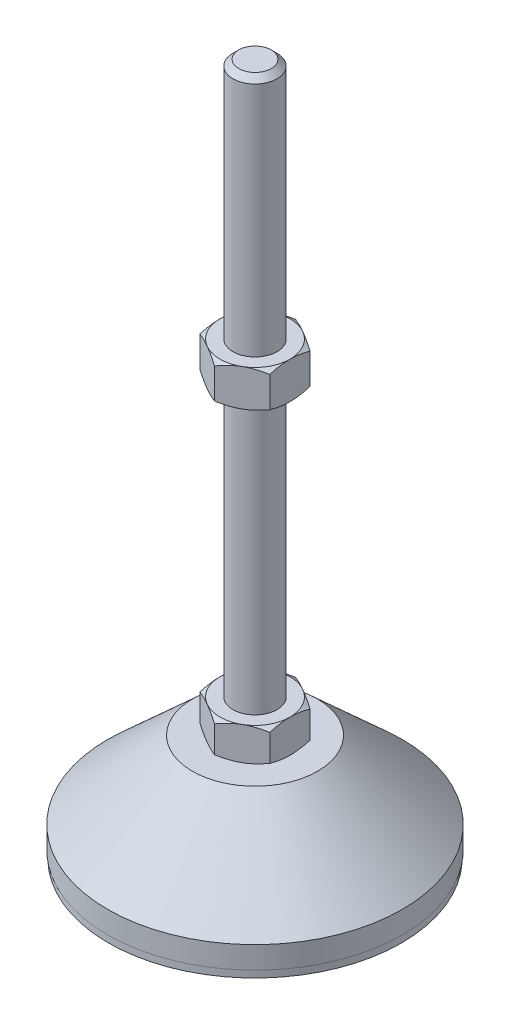
SolidWorks part; units mm, degrees
ref_plane "Спереди" through (0, 0, 0) normal (0, 0, 1) x (1, 0, 0)
ref_plane "Сверху" through (0, 0, 0) normal (0, 1, 0) x (1, 0, 0)
ref_plane "Справа" through (0, 0, 0) normal (1, 0, 0) x (0, 0, -1)
sketch "Эскиз1" plane through (0, 0, 0) normal (0, 0, 1) x (1, 0, 0)
  line L0 (0, 0) -> (-39.8, 0)
  line L1 (-39.8, 0) -> (-39.8, 2)
  line L2 (-39.8, 2) -> (-40, 2)
  line L3 (-40, 2) -> (-40, 8)
  line L4 (-40, 8) -> (-17, 29)
  line L5 (-17, 29) -> (-6, 29)
  line L12 (-6, 38) -> (-6, 186.4)
  line L13 (-6, 186.4) -> (-4.4, 188)
  line L14 (-4.4, 188) -> (0, 188)
  line L15 (0, 188) -> (0, 0) construction
  line L16 (-6, 29) -> (0, 29) construction
  line L17 (0, 0) -> (0, 188)
  line L18 (0, 0) -> (0, -7.9595) construction
  line L19 (-6, 38) -> (-6, 29)
  point P8 (-6, 112.2)
  point P23 (-11.5, 29)
  dimension "D1" = 12
  dimension "D2" = 29
  dimension "D3" = 9
  dimension "D4" = 80
  dimension "D5" = 6
  dimension "D6" = 1.6
  dimension "D7" = 45
  dimension "D8" = 34
  dimension "D9" = 2
  dimension "D10" = 150
  dimension "D11" = 6
  dimension "D12" = 0.2
revolve "Повернуть1" add sketch "Эскиз1" angle 360 about L17
sketch "Эскиз2" plane through (0, 29, 0) normal (0, 1, 0) x (1, 0, 0)
  line L1 (0, 10.9697) -> (-9.5, 5.4848)
  line L2 (-9.5, 5.4848) -> (-9.5, -5.4848)
  line L3 (-9.5, -5.4848) -> (0, -10.9697)
  line L4 (0, -10.9697) -> (9.5, -5.4848)
  line L5 (9.5, -5.4848) -> (9.5, 5.4848)
  line L6 (9.5, 5.4848) -> (0, 10.9697)
  circle A0 centre (0, 0) radius 9.5 construction
  dimension "D1" = 19
extrude "Бобышка-Вытянуть1" add sketch "Эскиз2" along normal up to vertex (9 mm away) up to point (-6, 38, 0)
ref_plane "Плоскость1" through (0, 112.2, 0) normal (0, 1, 0) x (1, 0, 0)
sketch "Эскиз3" plane through (0, 112.2, 0) normal (0, 1, 0) x (1, 0, 0)
  line L6 (9.5, 5.4848) -> (0, 10.9697)
  line L7 (0, 10.9697) -> (-9.5, 5.4848)
  line L8 (-9.5, 5.4848) -> (-9.5, -5.4848)
  line L9 (-9.5, -5.4848) -> (0, -10.9697)
  line L10 (0, -10.9697) -> (9.5, -5.4848)
  line L11 (9.5, -5.4848) -> (9.5, 5.4848)
  line L12 (9.5, 5.4848) -> (0, 10.9697)
  line L13 (0, 10.9697) -> (-9.5, 5.4848)
  line L14 (-9.5, 5.4848) -> (-9.5, -5.4848)
  line L15 (-9.5, -5.4848) -> (0, -10.9697)
  line L16 (0, -10.9697) -> (9.5, -5.4848)
  line L17 (9.5, -5.4848) -> (9.5, 5.4848)
  dimension "D1" = 0
extrude "Бобышка-Вытянуть2" add sketch "Эскиз3" along normal blind 10
sketch "Эскиз4" plane through (0, 0, 0) normal (0, 0, 1) x (1, 0, 0)
  line L0 (-9.5, 122.2) -> (-18.1603, 117.2)
  line L1 (-18.1603, 117.2) -> (-18.1603, 122.2)
  line L2 (-18.1603, 122.2) -> (-9.5, 122.2)
  line L3 (-18.1603, 117.2) -> (-9.5, 112.2)
  line L4 (50, 112.2) -> (-50, 112.2) construction
  line L5 (-9.5, 112.2) -> (-18.1603, 112.2)
  line L6 (-18.1603, 112.2) -> (-18.1603, 117.2)
  line L7 (-9.5, 122.2) -> (-9.5, 112.2) construction
  line L8 (-9.5, 38) -> (-17.2942, 38)
  line L9 (-17.2942, 38) -> (-17.2942, 33.5)
  line L10 (-17.2942, 33.5) -> (-9.5, 38)
  line L11 (-9.5, 29) -> (-17.2942, 33.5)
  line L12 (-17.2942, 33.5) -> (-17.2942, 29)
  line L13 (-17.2942, 29) -> (-9.5, 29)
  line L14 (0, 188) -> (0, 96.3793) construction
  dimension "D1" = 30
  dimension "D2" = 30
revolve "Вырез-Повернуть2" cut sketch "Эскиз4" angle 360 about L14
